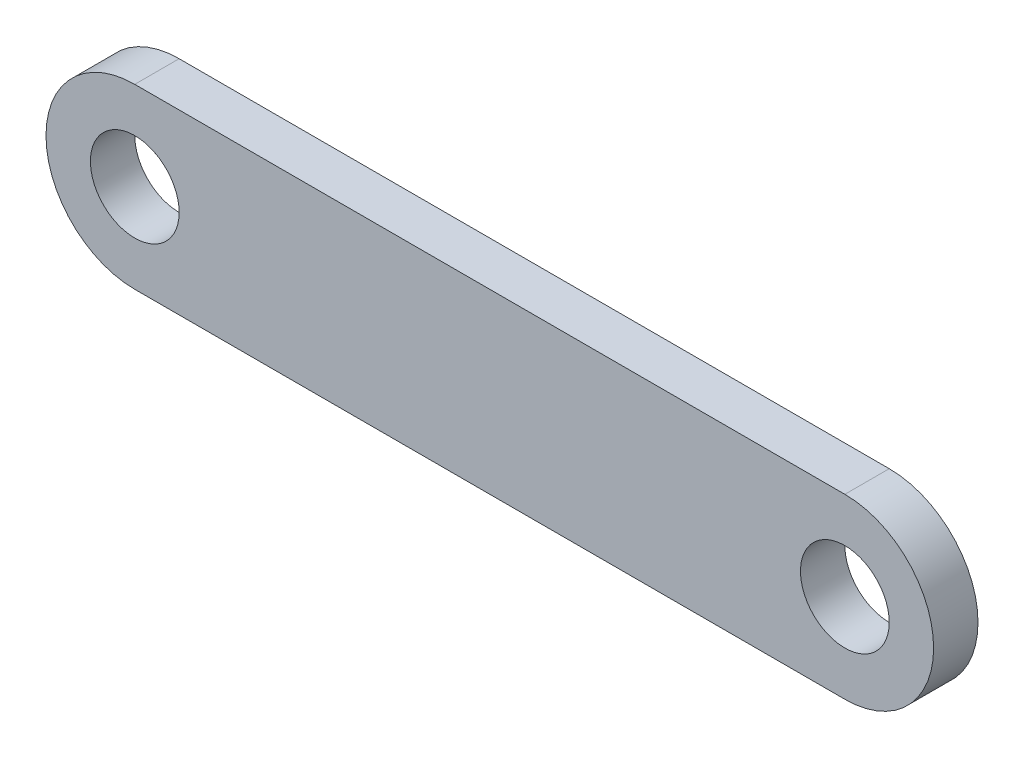
SolidWorks part; units mm, degrees
ref_plane "Front Plane" through (0, 0, 0) normal (0, 0, 1) x (1, 0, 0)
ref_plane "Top Plane" through (0, 0, 0) normal (0, 1, 0) x (1, 0, 0)
ref_plane "Right Plane" through (0, 0, 0) normal (1, 0, 0) x (0, 0, -1)
sketch "Sketch1" plane through (0, 0, 0) normal (0, 0, 1) x (1, 0, 0)
  line L0 (0, 0) -> (32, 0) construction
  line L1 (0, 4) -> (32, 4)
  line L2 (0, -4) -> (32, -4)
  arc A0 (0, 4) -> (0, -4) centre (0, 0) ccw
  arc A1 (32, -4) -> (32, 4) centre (32, 0) ccw
  circle A2 centre (0, 0) radius 2
  circle A3 centre (32, 0) radius 2
  point P3 (16, 0)
  dimension "D2" = 4
  dimension "D3" = 4
  dimension "D1" = 32
extrude "Boss-Extrude1" add sketch "Sketch1" along normal mid plane 2
